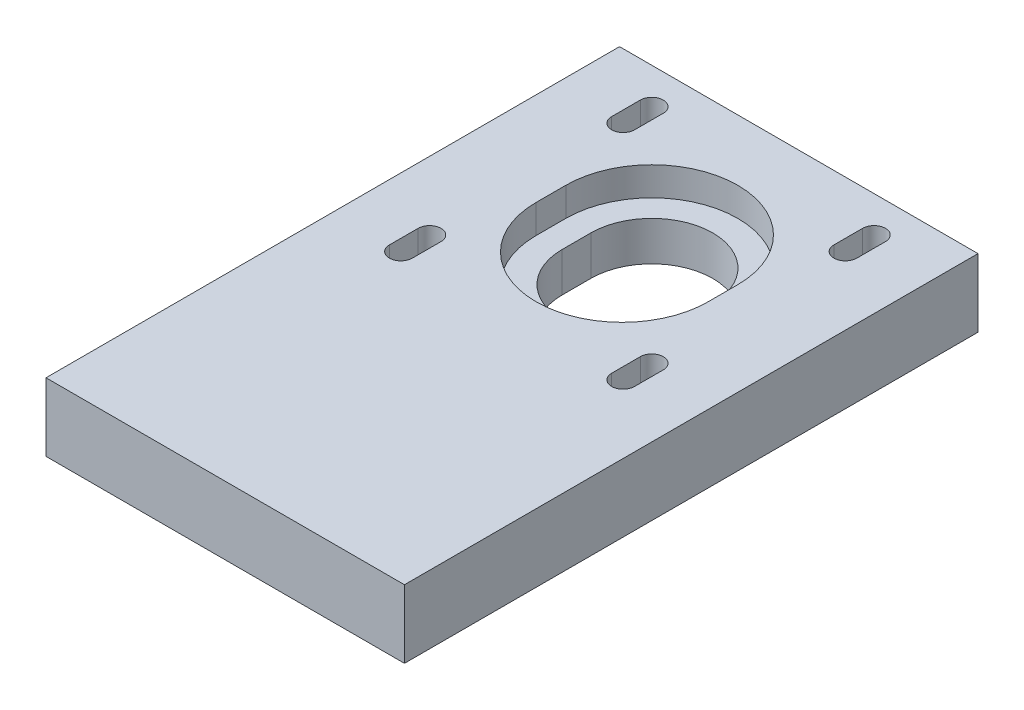
SolidWorks part; units mm, degrees
ref_plane "Front Plane" through (0, 0, 0) normal (0, 0, 1) x (1, 0, 0)
ref_plane "Top Plane" through (0, 0, 0) normal (0, 1, 0) x (1, 0, 0)
ref_plane "Right Plane" through (0, 0, 0) normal (1, 0, 0) x (0, 0, -1)
sketch "Sketch1" plane through (0, 0, 0) normal (0, 1, 0) x (1, 0, 0)
  line L1 (-25, -40) -> (25, -40)
  line L2 (-25, -40) -> (-25, 40)
  line L3 (-25, 40) -> (25, 40)
  line L4 (25, -40) -> (25, 40)
  line L5 (-25, -40) -> (25, 40) construction
  line L6 (-25, 40) -> (25, -40) construction
  point P0 (0, 0)
  dimension "D1" = 50
  dimension "D2" = 80
extrude "Boss-Extrude1" add sketch "Sketch1" along normal blind 9.5
sketch "Sketch2" plane through (0, 9.5, 0) normal (0, 1, 0) x (1, 0, 0)
  line L0 (0, 40) -> (0, -40) construction
  line L1 (25, 40) -> (-25, 40) construction
  line L2 (-25, -40) -> (25, -40) construction
  line L3 (-25, 35) -> (25, 35) construction
  line L4 (-25, 40) -> (-25, -40) construction
  line L5 (25, -40) -> (25, 40) construction
  line L6 (-25, 19.5) -> (25, 19.5) construction
  line L7 (-25, 4) -> (25, 4) construction
  line L8 (-15.5, 35) -> (-15.5, 31) construction
  line L9 (-13.9, 35) -> (-13.9, 31)
  line L10 (-17.1, 35) -> (-17.1, 31)
  line L11 (15.5, 35) -> (15.5, 31) construction
  line L12 (13.9, 35) -> (13.9, 31)
  line L13 (17.1, 35) -> (17.1, 31)
  line L14 (-15.5, 4) -> (-15.5, 0) construction
  line L15 (-13.9, 4) -> (-13.9, 0)
  line L16 (-17.1, 4) -> (-17.1, 0)
  line L17 (15.5, 4) -> (15.5, 0) construction
  line L18 (13.9, 4) -> (13.9, 0)
  line L19 (17.1, 4) -> (17.1, 0)
  line L20 (0, 19.5) -> (0, 15.5) construction
  line L21 (8.5, 19.5) -> (8.5, 15.5)
  line L22 (-8.5, 19.5) -> (-8.5, 15.5)
  arc A0 (13.9, 35) -> (17.1, 35) centre (15.5, 35) cw
  arc A1 (17.1, 31) -> (13.9, 31) centre (15.5, 31) cw
  arc A2 (-13.9, 4) -> (-17.1, 4) centre (-15.5, 4) ccw
  arc A3 (-17.1, 0) -> (-13.9, 0) centre (-15.5, 0) ccw
  arc A4 (-13.9, 35) -> (-17.1, 35) centre (-15.5, 35) ccw
  arc A5 (-17.1, 31) -> (-13.9, 31) centre (-15.5, 31) ccw
  arc A6 (13.9, 4) -> (17.1, 4) centre (15.5, 4) cw
  arc A7 (17.1, 0) -> (13.9, 0) centre (15.5, 0) cw
  arc A8 (8.5, 19.5) -> (-8.5, 19.5) centre (0, 19.5) ccw
  arc A9 (-8.5, 15.5) -> (8.5, 15.5) centre (0, 15.5) ccw
  point P15 (15.5, 33)
  point P24 (-15.5, 33)
  point P33 (15.5, 2)
  point P38 (-15.5, 2)
  point P46 (0, 17.5)
  dimension "D1" = 1.6
  dimension "D6" = 8.5
  dimension "D2" = 15.5
  dimension "D3" = 15.5
  dimension "D4" = 5
  dimension "D5" = 4
  dimension "D7" = 4
extrude "Cut-Extrude1" cut sketch "Sketch2" against normal through all
sketch "Sketch3" plane through (0, 9.5, 0) normal (0, 1, 0) x (1, 0, 0)
  line L0 (0, 19.5) -> (0, 15.3588) construction
  line L1 (12, 19.5) -> (12, 15.3588)
  line L2 (-12, 19.5) -> (-12, 15.3588)
  arc A0 (12, 19.5) -> (-12, 19.5) centre (0, 19.5) ccw
  arc A1 (-12, 15.3588) -> (12, 15.3588) centre (0, 15.3588) ccw
  point P4 (0, 17.4294)
  dimension "D1" = 12
extrude "Cut-Extrude2" cut sketch "Sketch3" against normal blind 4
